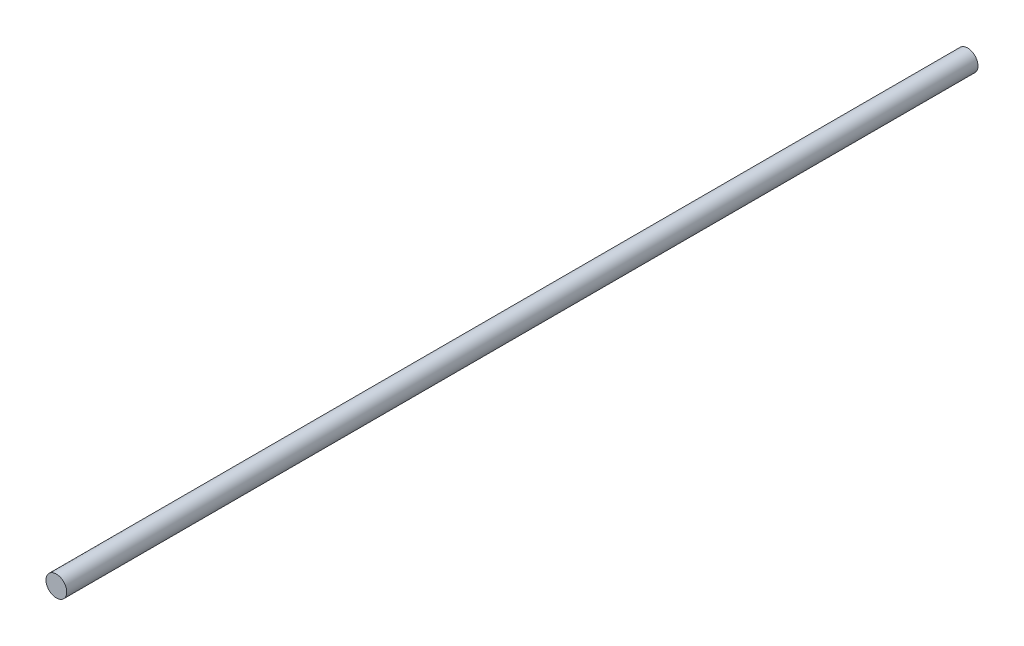
SolidWorks part; units mm, degrees
ref_plane "前视基准面" through (0, 0, 0) normal (0, 0, 1) x (1, 0, 0)
ref_plane "上视基准面" through (0, 0, 0) normal (0, 1, 0) x (1, 0, 0)
ref_plane "右视基准面" through (0, 0, 0) normal (1, 0, 0) x (0, 0, -1)
other "Configuration Table"
sketch "草图2" plane through (0, 0, 0) normal (0, 0, 1) x (1, 0, 0)
  circle A0 centre (0, 0) radius 2.052
  point P3 (2.05, 0.0899)
  dimension "D1" = 2.05
extrude "凸台-拉伸1" add sketch "草图2" along normal blind 180
